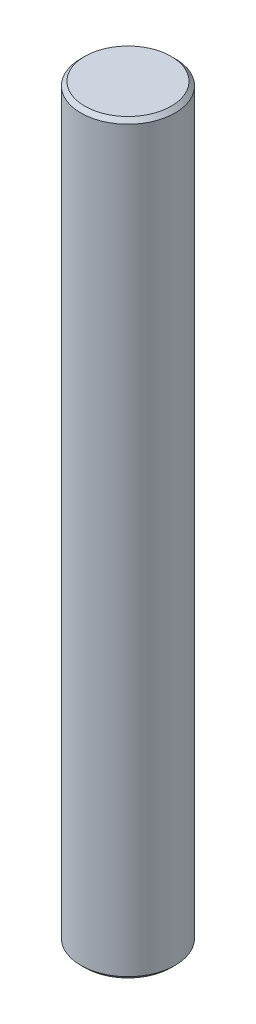
SolidWorks part; units mm, degrees
ref_plane "Front Plane" through (0, 0, 0) normal (0, 0, 1) x (1, 0, 0)
ref_plane "Top Plane" through (0, 0, 0) normal (0, 1, 0) x (1, 0, 0)
ref_plane "Right Plane" through (0, 0, 0) normal (1, 0, 0) x (0, 0, -1)
sketch "Sketch1" plane through (0, 0, 0) normal (0, 1, 0) x (1, 0, 0)
  circle A0 centre (0, 0) radius 6
  dimension "D1" = 12
extrude "Boss-Extrude1" add sketch "Sketch1" along normal blind 95
chamfer "Chamfer1" distance 0.5 angle 45 2 edges at (0, 0, 6) (0, 95, 6)
